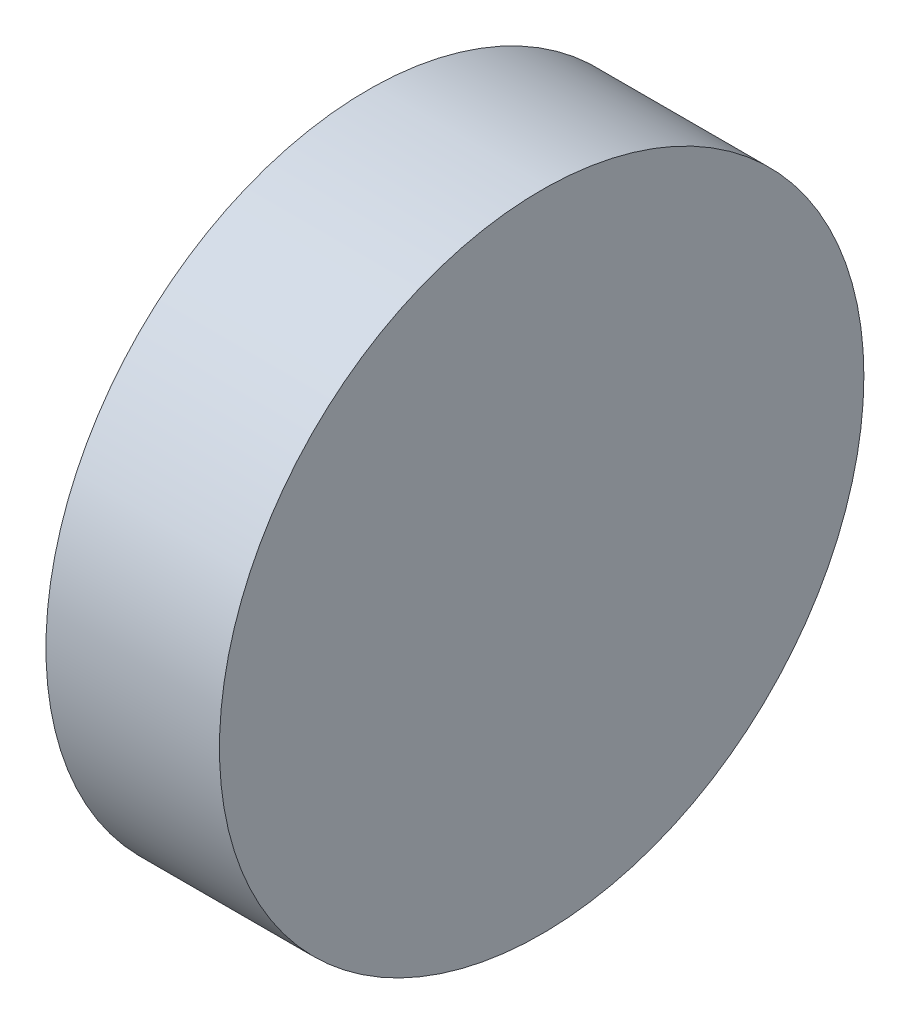
SolidWorks part; units mm, degrees
ref_plane "Front Plane" through (0, 0, 0) normal (0, 0, 1) x (1, 0, 0)
ref_plane "Top Plane" through (0, 0, 0) normal (0, 1, 0) x (1, 0, 0)
ref_plane "Right Plane" through (0, 0, 0) normal (1, 0, 0) x (0, 0, -1)
sketch "Sketch3" plane through (0, 0, 0) normal (1, 0, 0) x (0, 0, -1)
  circle A0 centre (0, 0) radius 165.1
  dimension "D1" = 330.2
extrude "Boss-Extrude3" add sketch "Sketch3" along normal blind 88.9
